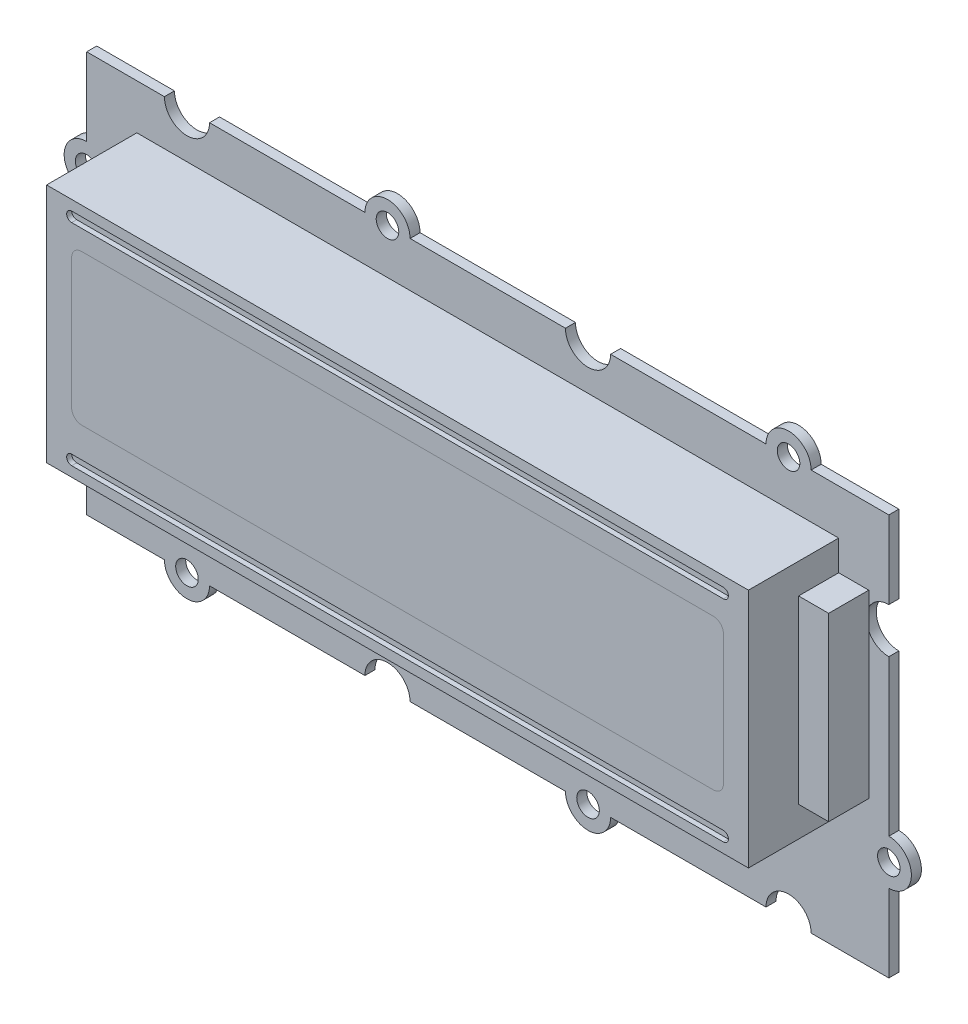
SolidWorks part; units mm, degrees
ref_plane "Plan de face" through (0, 0, 0) normal (0, 0, 1) x (1, 0, 0)
ref_plane "Plan de dessus" through (0, 0, 0) normal (0, 1, 0) x (1, 0, 0)
ref_plane "Plan de droite" through (0, 0, 0) normal (1, 0, 0) x (0, 0, -1)
sketch "Esquisse1" plane through (0, 0, 0) normal (0, 0, 1) x (1, 0, 0)
  line L0 (0, 30.9281) -> (0, -19.2371) construction
  line L1 (-46.5895, 0) -> (45.4509, 0) construction
  line L2 (-40, 20) -> (-32.25, 20)
  line L3 (-40, 20) -> (-40, 12.25)
  line L4 (-40, -20) -> (-32.25, -20)
  line L5 (40, 20) -> (40, 12.25)
  line L6 (30, 26.2841) -> (30, 14.2511) construction
  line L7 (10, 26.2841) -> (10, 14.2511) construction
  line L8 (-10, 26.2841) -> (-10, 14.2511) construction
  line L9 (-30, 26.2841) -> (-30, 14.2511) construction
  line L10 (32.3167, 10) -> (43.8027, 10) construction
  line L11 (-34.8317, 10) -> (-45.1683, 10) construction
  line L12 (-27.75, 20) -> (-12.25, 20)
  line L13 (-7.75, 20) -> (7.75, 20)
  line L14 (32.25, 20) -> (40, 20)
  line L15 (12.25, 20) -> (27.75, 20)
  line L16 (40, 7.75) -> (40, -7.75)
  line L17 (40, -12.25) -> (40, -20)
  line L18 (32.25, -20) -> (40, -20)
  line L19 (12.25, -20) -> (27.75, -20)
  line L20 (-7.75, -20) -> (7.75, -20)
  line L21 (-27.75, -20) -> (-12.25, -20)
  line L22 (-40, -12.25) -> (-40, -20)
  line L23 (-40, 7.75) -> (-40, -7.75)
  arc A0 (-40, 12.25) -> (-40, 7.75) centre (-40, 10) ccw
  arc A1 (-32.25, 20) -> (-27.75, 20) centre (-30, 20) ccw
  arc A2 (-7.75, 20) -> (-12.25, 20) centre (-10, 20) ccw
  arc A3 (7.75, 20) -> (12.25, 20) centre (10, 20) ccw
  arc A4 (32.25, 20) -> (27.75, 20) centre (30, 20) ccw
  arc A5 (40, 12.25) -> (40, 7.75) centre (40, 10) ccw
  circle A7 centre (-10, 20) radius 1.125
  circle A9 centre (30, 20) radius 1.125
  circle A11 centre (-40, 10) radius 1.125
  circle A12 centre (40, -10) radius 1.125
  arc A13 (40, -7.75) -> (40, -12.25) centre (40, -10) cw
  arc A15 (27.75, -20) -> (32.25, -20) centre (30, -20) cw
  circle A16 centre (10, -20) radius 1.125
  arc A17 (12.25, -20) -> (7.75, -20) centre (10, -20) cw
  arc A19 (-12.25, -20) -> (-7.75, -20) centre (-10, -20) cw
  circle A20 centre (-30, -20) radius 1.125
  arc A21 (-27.75, -20) -> (-32.25, -20) centre (-30, -20) cw
  arc A23 (-40, -7.75) -> (-40, -12.25) centre (-40, -10) cw
  dimension "D9" = 4.5
  dimension "D10" = 4.5
  dimension "D11" = 4.5
  dimension "D12" = 4.5
  dimension "D13" = 4.5
  dimension "D14" = 4.5
  dimension "D15" = 2.25
  dimension "D16" = 2.25
  dimension "D17" = 2.25
  dimension "D18" = 2.25
  dimension "D19" = 2.25
  dimension "D20" = 2.25
  dimension "D1" = 80
  dimension "D2" = 40
  dimension "D3" = 20
  dimension "D4" = 20
  dimension "D5" = 20
  dimension "D6" = 10
  dimension "D7" = 10
  dimension "D8" = 10
extrude "Boss.-Extru.1" add sketch "Esquisse1" along normal blind 1
sketch "Esquisse2" plane through (0, 0, 1) normal (0, 0, 1) x (1, 0, 0)
  line L0 (0, -23.7129) -> (0, 24.4015) construction
  line L1 (-35, 15.5) -> (35, 15.5)
  line L2 (-35, 15.5) -> (-35, -8.5)
  line L3 (-35, -8.5) -> (35, -8.5)
  line L4 (35, 15.5) -> (35, -8.5)
  line L5 (-31.5, 11.5) -> (31.5, 11.5)
  line L6 (-32.5, 10.5) -> (-32.5, -2.5)
  line L7 (-31.5, -3.5) -> (31.5, -3.5)
  line L8 (32.5, 10.5) -> (32.5, -2.5)
  line L9 (-32.25, 20) -> (-40, 20) construction
  arc A0 (31.5, -3.5) -> (32.5, -2.5) centre (31.5, -2.5) ccw
  arc A1 (31.5, 11.5) -> (32.5, 10.5) centre (31.5, 10.5) cw
  arc A2 (-32.5, -2.5) -> (-31.5, -3.5) centre (-31.5, -2.5) ccw
  arc A3 (-31.5, 11.5) -> (-32.5, 10.5) centre (-31.5, 10.5) ccw
  dimension "D7" = 1
  dimension "D1" = 70
  dimension "D2" = 24
  dimension "D3" = 4
  dimension "D4" = 15
  dimension "D5" = 65
  dimension "D6" = 4.5
extrude "Boss.-Extru.2" add sketch "Esquisse2" along normal blind 9
sketch "Esquisse3" plane through (0, 0, 10) normal (0, 0, 1) x (1, 0, 0)
  line L0 (0, -23.3686) -> (0, 26.295) construction
  line L2 (-32.5, 14.5) -> (32.5, 14.5)
  line L3 (-32.5, 13.2271) -> (-32.5, 14.6724) construction
  line L4 (-32.5, 13.5) -> (32.5, 13.5)
  line L5 (32.5, 13.1751) -> (32.5, 14.8249) construction
  line L6 (31.5, 11.5) -> (-31.5, 11.5) construction
  line L7 (-44.4775, 3.5) -> (44.11, 3.5) construction
  line L8 (35, 15.5) -> (-35, 15.5) construction
  line L9 (-35, -8.5) -> (35, -8.5) construction
  line L10 (32.5, -6.1751) -> (32.5, -7.8249) construction
  line L11 (-32.5, -6.2271) -> (-32.5, -7.6724) construction
  line L12 (-32.5, -6.5) -> (32.5, -6.5)
  line L13 (-32.5, -7.5) -> (32.5, -7.5)
  arc A0 (-32.5, 14.5) -> (-32.5, 13.5) centre (-32.5, 14) ccw
  arc A1 (32.5, 13.5) -> (32.5, 14.5) centre (32.5, 14) ccw
  arc A2 (32.5, -6.5) -> (32.5, -7.5) centre (32.5, -7) cw
  arc A3 (-32.5, -7.5) -> (-32.5, -6.5) centre (-32.5, -7) cw
  dimension "D1" = 65
  dimension "D2" = 1
  dimension "D3" = 2
extrude "Enlèv. mat.-Extru.1" cut sketch "Esquisse3" against normal blind 0.5
sketch "Esquisse4" plane through (0, 0, 10) normal (0, 0, 1) x (1, 0, 0)
  line L0 (32.5, -2.5) -> (32.5, 10.5) construction
  line L1 (-32.5, 10.5) -> (-32.5, -2.5) construction
  line L2 (-31.5, -3.5) -> (31.5, -3.5) construction
  line L3 (31.5, 11.5) -> (-31.5, 11.5) construction
  line L12 (32.5, -2.5) -> (32.5, 10.5)
  line L13 (-32.5, 10.5) -> (-32.5, -2.5)
  line L14 (-31.5, -3.5) -> (31.5, -3.5)
  line L15 (31.5, 11.5) -> (-31.5, 11.5)
  arc A0 (-31.5, 11.5) -> (-32.5, 10.5) centre (-31.5, 10.5) ccw construction
  arc A1 (-32.5, -2.5) -> (-31.5, -3.5) centre (-31.5, -2.5) ccw construction
  arc A2 (31.5, -3.5) -> (32.5, -2.5) centre (31.5, -2.5) ccw construction
  arc A3 (32.5, 10.5) -> (31.5, 11.5) centre (31.5, 10.5) ccw construction
  arc A4 (-31.5, 11.5) -> (-32.5, 10.5) centre (-31.5, 10.5) ccw
  arc A5 (-32.5, -2.5) -> (-31.5, -3.5) centre (-31.5, -2.5) ccw
  arc A6 (31.5, -3.5) -> (32.5, -2.5) centre (31.5, -2.5) ccw
  arc A7 (32.5, 10.5) -> (31.5, 11.5) centre (31.5, 10.5) ccw
extrude "Boss.-Extru.4" add sketch "Esquisse4" against normal blind 1 separate body
sketch "Esquisse5" plane through (35, 0, 0) normal (1, 0, 0) x (0, 0, -1)
  line L1 (-1, -8.5) -> (-1, 15.5) construction
  line L2 (-1, 12.5) -> (-5, 12.5)
  line L3 (-1, 12.5) -> (-1, -5.5)
  line L4 (-1, -5.5) -> (-5, -5.5)
  line L7 (-5, 12.5) -> (-5, -5.5)
  line L8 (5.1616, 3.5) -> (-17.1184, 3.5) construction
  line L9 (-10, 15.5) -> (-1, 15.5) construction
  line L10 (-10, -8.5) -> (-1, -8.5) construction
  point P6 (-3, 12.5)
  point P13 (-3, -5.5)
  dimension "D1" = 18
  dimension "D2" = 4
extrude "Boss.-Extru.5" add sketch "Esquisse5" along normal blind 3
